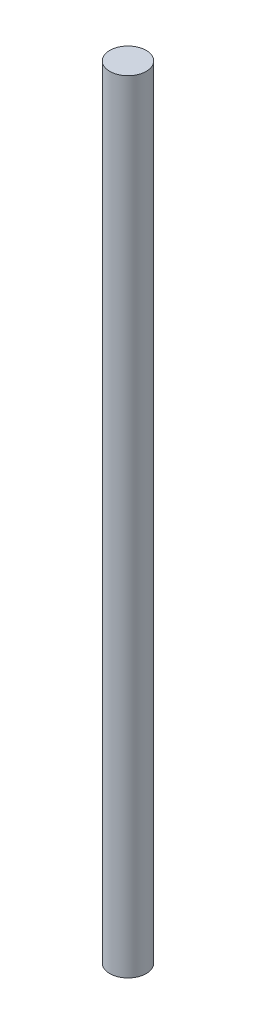
SolidWorks part; units mm, degrees
ref_plane "Front Plane" through (0, 0, 0) normal (0, 0, 1) x (1, 0, 0)
ref_plane "Top Plane" through (0, 0, 0) normal (0, 1, 0) x (1, 0, 0)
ref_plane "Right Plane" through (0, 0, 0) normal (1, 0, 0) x (0, 0, -1)
sketch "Sketch2" plane through (0, 0, 0) normal (0, 1, 0) x (1, 0, 0)
  circle A0 centre (0, 0) radius 2.3685
  dimension "D1" = 4.7371
extrude "Boss-Extrude1" add sketch "Sketch2" along normal blind 101.6
